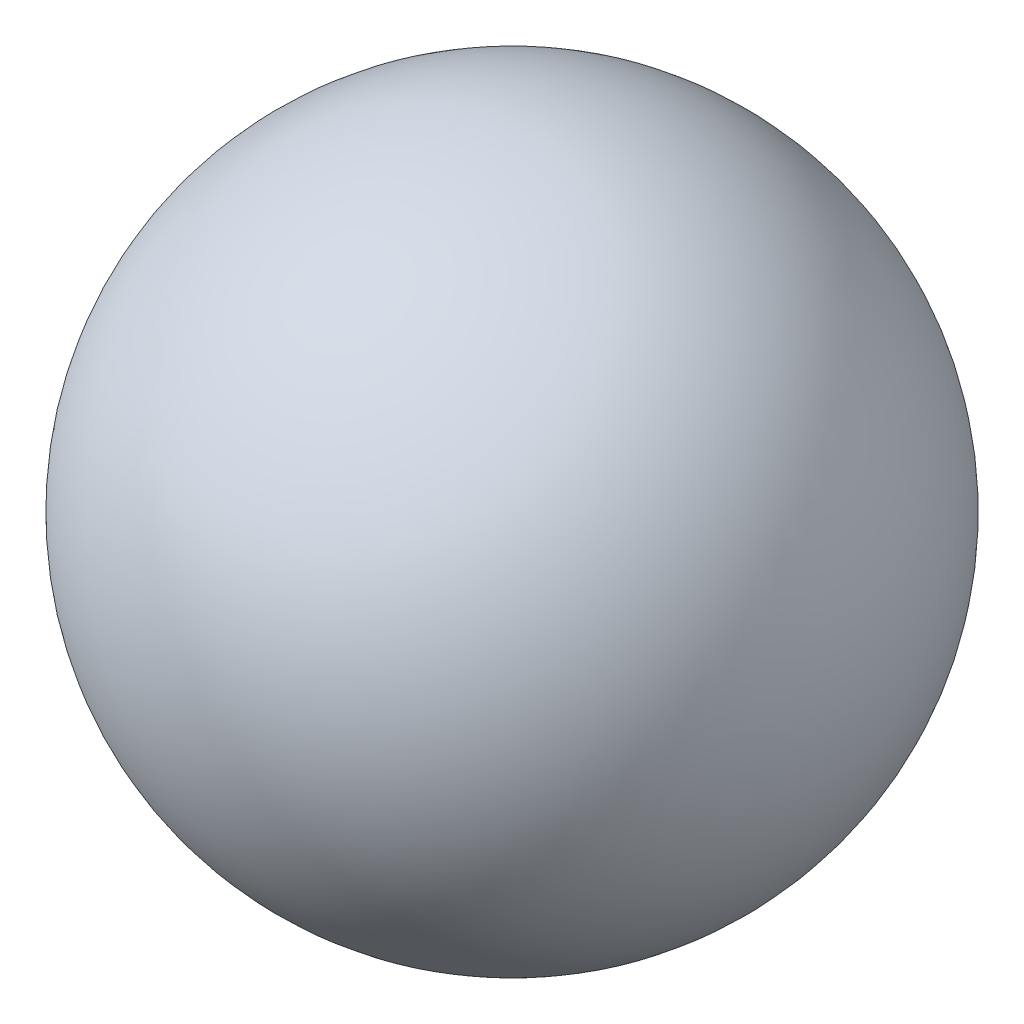
SolidWorks part; units mm, degrees
ref_plane "Front Plane" through (0, 0, 0) normal (0, 0, 1) x (1, 0, 0)
ref_plane "Top Plane" through (0, 0, 0) normal (0, 1, 0) x (1, 0, 0)
ref_plane "Right Plane" through (0, 0, 0) normal (1, 0, 0) x (0, 0, -1)
sketch "PingPongBallSketch" plane through (0, 0, 0) normal (0, 0, 1) x (1, 0, 0)
  line L0 (0, 20) -> (0, 19)
  line L1 (0, -19) -> (0, -20)
  line L2 (0, 15.0191) -> (0, -14.1352) construction
  arc A0 (0, 20) -> (0, -20) centre (0, 0) cw
  arc A1 (0, 19) -> (0, -19) centre (0, 0) cw
  dimension "D1" = 20
  dimension "D2" = 19
revolve "PingPongBall" add sketch "PingPongBallSketch" angle 360 about L2
